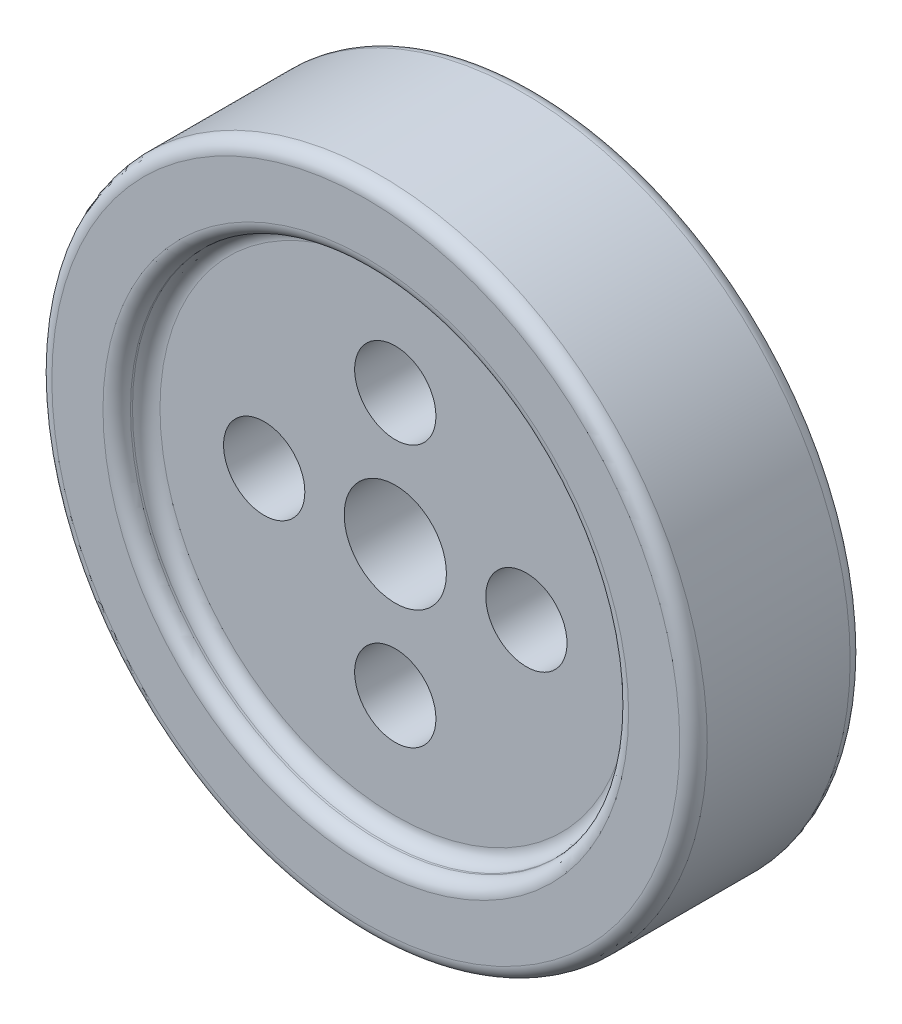
SolidWorks part; units mm, degrees
ref_plane "Front Plane" through (0, 0, 0) normal (0, 0, 1) x (1, 0, 0)
ref_plane "Top Plane" through (0, 0, 0) normal (0, 1, 0) x (1, 0, 0)
ref_plane "Right Plane" through (0, 0, 0) normal (1, 0, 0) x (0, 0, -1)
sketch "Sketch2" plane through (0, 0, 0) normal (0, 0, 1) x (1, 0, 0)
  circle A0 centre (0, 0) radius 250
  dimension "D1" = 500
extrude "Boss-Extrude1" add sketch "Sketch2" along normal blind 130
sketch "Sketch3" plane through (0, 0, 130) normal (0, 0, 1) x (1, 0, 0)
  circle A0 centre (0, 0) radius 190
  circle A1 centre (0, 0) radius 250 construction
  dimension "D1" = 380
extrude "Cut-Extrude1" cut sketch "Sketch3" against normal mid plane 45
fillet "Fillet5" radius 10.5 2 edges at (190, 0, 107.5) (190, 0, 130)
fillet "Fillet6" radius 10.5 1 edges at (250, 0, 130)
sketch "Sketch4" plane through (0, 0, 0) normal (0, 0, -1) x (-1, 0, 0)
  circle A0 centre (0, 0) radius 190
  dimension "D1" = 380
extrude "Cut-Extrude2" cut sketch "Sketch4" against normal mid plane 45
fillet "Fillet7" radius 10.5 3 edges at (-190, 0, 22.5) (250, 0, 0) (190, 0, 0)
sketch "Sketch5" plane through (0, 0, 107.5) normal (0, 0, 1) x (1, 0, 0)
  circle A0 centre (0, 0) radius 100
  circle A1 centre (0, 100) radius 31
  circle A2 centre (100, 0) radius 31
  circle A3 centre (0, -100) radius 31
  circle A4 centre (-100, 0) radius 31
  circle A5 centre (0, 0) radius 39
  circle A6 centre (0, 0) radius 179.5 construction
  point P14 (0, 0)
  dimension "D1" = 200
  dimension "D2" = 4
  dimension "D3" = 62
  dimension "D6" = 78
extrude "Cut-Extrude3" cut sketch "Sketch5" against normal through all contours A0 A4 | A0 A4 | A0 A1 | A0 A1 | A0 A2 | A0 A2 | A0 A3 | A0 A3
sketch "Sketch6" plane through (0, 0, 107.5) normal (0, 0, 1) x (1, 0, 0)
  circle A0 centre (0, 0) radius 39
extrude "Cut-Extrude4" cut sketch "Sketch6" against normal through all
